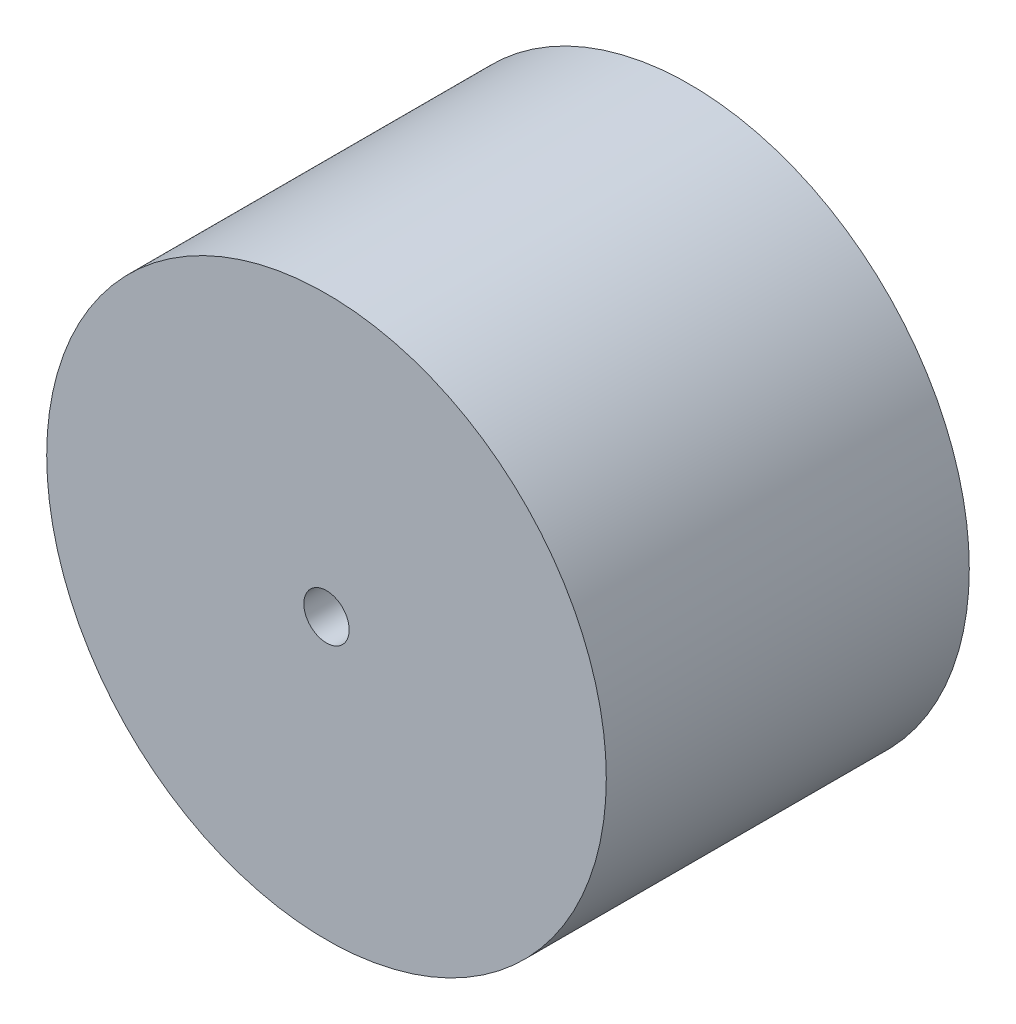
SolidWorks part; units mm, degrees
ref_plane "前视基准面" through (0, 0, 0) normal (0, 0, 1) x (1, 0, 0)
ref_plane "上视基准面" through (0, 0, 0) normal (0, 1, 0) x (1, 0, 0)
ref_plane "右视基准面" through (0, 0, 0) normal (1, 0, 0) x (0, 0, -1)
sketch "草图1" plane through (0, 0, 0) normal (0, 0, 1) x (1, 0, 0)
  circle A0 centre (0, 0) radius 18.5
  dimension "D1" = 37
extrude "凸台-拉伸1" add sketch "草图1" along normal blind 24
sketch "草图2" plane through (0, 0, 24) normal (0, 0, 1) x (1, 0, 0)
  circle A1 centre (0, 0) radius 1.5
  dimension "D1" = 3
extrude "切除-拉伸1" cut sketch "草图2" against normal through all
